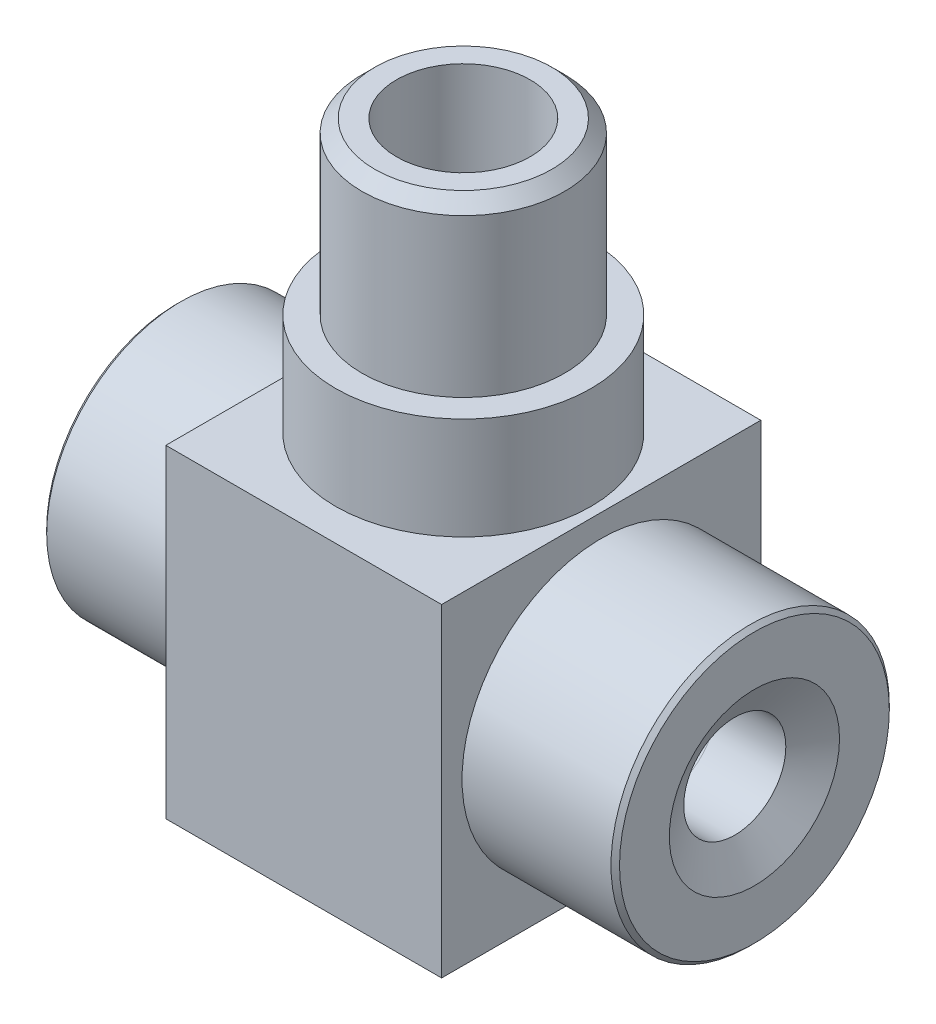
SolidWorks part; units mm, degrees
ref_plane "Спереди" through (0, 0, 0) normal (0, 0, 1) x (1, 0, 0)
ref_plane "Сверху" through (0, 0, 0) normal (0, 1, 0) x (1, 0, 0)
ref_plane "Справа" through (0, 0, 0) normal (1, 0, 0) x (0, 0, -1)
sketch "Эскиз1" plane through (0, 0, 0) normal (0, 0, 1) x (1, 0, 0)
  line L1 (0, 0) -> (32.4, 0)
  line L2 (0, 0) -> (0, 38)
  line L3 (0, 38) -> (32.4, 38)
  line L4 (32.4, 0) -> (32.4, 38)
  dimension "D1" = 32.4
  dimension "D2" = 38
extrude "Бобышка-Вытянуть1" add sketch "Эскиз1" along normal blind 37.5
sketch "Эскиз4" plane through (0, 0, 0) normal (-1, 0, 0) x (0, 0, 1)
  line L0 (18.75, 38) -> (18.75, 0) construction
  line L1 (37.5, 38) -> (0, 38) construction
  line L2 (37.5, 0) -> (0, 0) construction
  line L3 (0, 19) -> (37.5, 19) construction
  line L4 (0, 38) -> (0, 0) construction
  line L5 (37.5, 38) -> (37.5, 0) construction
  circle A0 centre (18.75, 19) radius 15.75
  dimension "D1" = 31.5
extrude "Бобышка-Вытянуть2" add sketch "Эскиз4" along normal blind 17.5
sketch "Эскиз5" plane through (-17.5, 0, 0) normal (-1, 0, 0) x (0, 0, 1)
  circle A0 centre (18.75, 19) radius 9.3
  dimension "D1" = 18.6
extrude "Вырез-Вытянуть1" cut sketch "Эскиз5" against normal blind 18
cosmetic thread "Условное изображение резьбы4" parameters "D1"=18, "D2"=20
sketch "Эскиз6" plane through (0.5, 0, 0) normal (-1, 0, 0) x (0, 0, 1)
  circle A0 centre (18.75, 19) radius 4
  dimension "D1" = 8
extrude "Вырез-Вытянуть2" cut sketch "Эскиз6" against normal blind 2.4
sketch "Эскиз7" plane through (0.5, 0, 0) normal (-1, 0, 0) x (0, 0, 1)
  line L0 (18.75, 19) -> (18.75, 11.2413) construction
  circle A0 centre (18.75, 15) radius 2
  dimension "D2" = 4
  dimension "D1" = 4
extrude "Вырез-Вытянуть3" cut sketch "Эскиз7" against normal blind 18.6
sketch "Эскиз8" plane through (32.4, 0, 0) normal (1, 0, 0) x (0, 0, -1)
  line L0 (0, 0) -> (0, 38) construction
  line L1 (0, 19) -> (-37.5, 19) construction
  line L2 (-37.5, 0) -> (-37.5, 38) construction
  line L3 (-18.75, 38) -> (-18.75, 0) construction
  line L4 (-37.5, 38) -> (0, 38) construction
  line L5 (-37.5, 0) -> (0, 0) construction
  circle A0 centre (-18.75, 19) radius 16.35
  dimension "D1" = 32.7
extrude "Бобышка-Вытянуть3" add sketch "Эскиз8" along normal blind 18
cosmetic thread "Условное изображение резьбы3" parameters "D1"=14.4, "D2"=22.376
sketch "Эскиз9" plane through (50.4, 0, 0) normal (1, 0, 0) x (0, 0, -1)
  circle A0 centre (-18.75, 19) radius 6
  dimension "D1" = 12
extrude "Вырез-Вытянуть4" cut sketch "Эскиз9" against normal blind 12.5
chamfer "Фаска1" distance 4 angle 30 1 edges at (50.4, 19, 12.75)
sketch "Эскиз10" plane through (37.9, 0, 0) normal (1, 0, 0) x (0, 0, -1)
  circle A0 centre (-18.75, 19) radius 2.5
  dimension "D1" = 5
extrude "Вырез-Вытянуть5" cut sketch "Эскиз10" against normal blind 21.7 contours A0
fillet "Скругление1" radius 2 1 edges at (37.9, 19, 12.75)
sketch "Эскиз11" plane through (0, 38, 0) normal (0, 1, 0) x (1, 0, 0)
  line L0 (0, 0) -> (32.4, -37.5) construction
  line L1 (0, -37.5) -> (32.4, 0) construction
  circle A0 centre (16.2, -18.75) radius 15
  dimension "D1" = 30
extrude "Бобышка-Вытянуть4" add sketch "Эскиз11" along normal blind 12
sketch "Эскиз12" plane through (0, 50, 0) normal (0, 1, 0) x (1, 0, 0)
  circle A0 centre (16.2, -18.75) radius 11.9
  dimension "D1" = 23.8
extrude "Бобышка-Вытянуть5" add sketch "Эскиз12" along normal blind 20
cosmetic thread "Условное изображение резьбы1" parameters "D1"=16.4, "D2"=22.376
sketch "Эскиз13" plane through (0, 70, 0) normal (0, 1, 0) x (1, 0, 0)
  circle A0 centre (16.2, -18.75) radius 7.85
  dimension "D1" = 15.7
extrude "Вырез-Вытянуть6" cut sketch "Эскиз13" against normal blind 17
sketch "Эскиз14" plane through (0, 53, 0) normal (0, 1, 0) x (1, 0, 0)
  circle A0 centre (16.2, -18.75) radius 4.5
  dimension "D1" = 9
extrude "Вырез-Вытянуть7" cut sketch "Эскиз14" against normal blind 42
cosmetic thread "Условное изображение резьбы5" parameters "D1"=37, "D2"=18
chamfer "Фаска2" distance 1.5 angle 45 1 edges at (16.2, 70, 30.65)
chamfer "Фаска4" distance 0.5 angle 45 1 edges at (-17.5, 19, 34.5)
chamfer "Фаска5" distance 0.5 angle 45 1 edges at (50.4, 19, 2.4)
sketch "Эскиз15" plane through (0, 11, 0) normal (0, 1, 0) x (1, 0, 0)
  circle A0 centre (16.2, -18.75) radius 3.5
  dimension "D1" = 7
extrude "Вырез-Вытянуть8" cut sketch "Эскиз15" against normal blind 6
chamfer "Фаска6" distance 5 angle 26.57 1 edges at (16.2, 5, 22.25)
